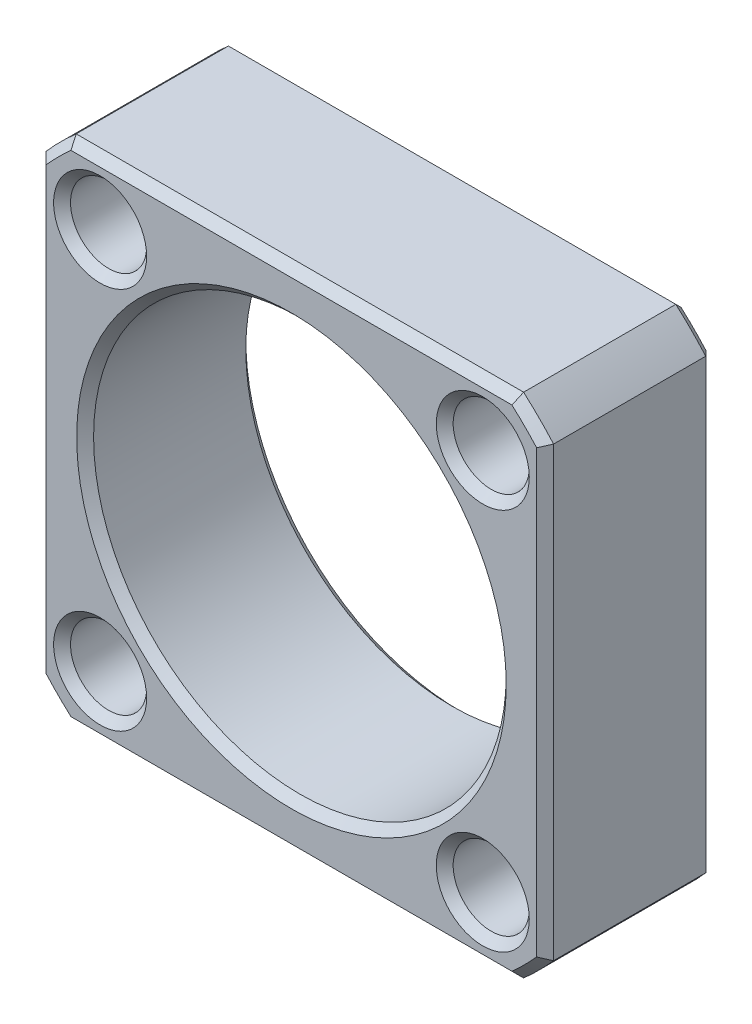
SolidWorks part; units mm, degrees
material "6061 Alloy"
ref_plane "Front Plane" through (0, 0, 0) normal (0, 0, 1) x (1, 0, 0)
ref_plane "Top Plane" through (0, 0, 0) normal (0, 1, 0) x (1, 0, 0)
ref_plane "Right Plane" through (0, 0, 0) normal (1, 0, 0) x (0, 0, -1)
sketch "Sketch1" plane through (0, 0, 0) normal (0, 0, 1) x (1, 0, 0)
  line L0 (-13.2288, 15) -> (13.2288, 15)
  line L1 (-20, 0) -> (20, 0) construction
  line L2 (-13.2288, -15) -> (13.2288, -15)
  line L3 (-15, 13.2288) -> (-15, -13.2288)
  line L4 (0, 15) -> (0, 0) construction
  line L5 (15, 13.2288) -> (15, -13.2288)
  arc A0 (-13.2288, 15) -> (-15, 13.2288) centre (0, 0) ccw
  arc A1 (13.2288, -15) -> (15, -13.2288) centre (0, 0) ccw
  circle A2 centre (0, 0) radius 16 construction
  circle A3 centre (-16, 0) radius 2.25 construction
  circle A4 centre (-11.3137, 11.3137) radius 2.25
  circle A5 centre (0, 16) radius 2.25 construction
  circle A6 centre (11.3137, 11.3137) radius 2.25
  circle A7 centre (16, 0) radius 2.25 construction
  circle A8 centre (11.3137, -11.3137) radius 2.25
  circle A9 centre (0, -16) radius 2.25 construction
  circle A10 centre (-11.3137, -11.3137) radius 2.25
  arc A11 (-15, -13.2288) -> (-13.2288, -15) centre (0, 0) ccw
  arc A12 (15, 13.2288) -> (13.2288, 15) centre (0, 0) ccw
  point P27 (0, 0)
  dimension "D1" = 40
  dimension "D3" = 32
  dimension "D5" = 4.5
  dimension "D2" = 15
  dimension "D6" = 30
  dimension "D4" = 8
extrude "Boss-Extrude1" add sketch "Sketch1" along normal blind 10
sketch "Sketch2" plane through (0, 0, 10) normal (0, 0, 1) x (1, 0, 0)
  circle A0 centre (0, 0) radius 12.2
  dimension "D1" = 24.4
extrude "Cut-Extrude3" cut sketch "Sketch2" against normal through all
chamfer "Chamfer1" distance 0.5 angle 45 26 edges at (-9.0637, -11.3137, 0) (13.5637, 11.3137, 0) (-15, 0, 0) (-14.1421, -14.1421, 0) (0, -15, 0) (14.1421, -14.1421, 0) (15, 0, 0) (14.1421, 14.1421, 0) (0, 15, 0) (-14.1421, 14.1421, 0) (-9.0637, 11.3137, 0) (13.5637, -11.3137, 0) (12.2, 0, 0) (-9.0637, -11.3137, 10) (13.5637, 11.3137, 10) (0, 15, 10) (14.1421, 14.1421, 10) (15, 0, 10) (14.1421, -14.1421, 10) (0, -15, 10) (-14.1421, -14.1421, 10) (-15, 0, 10) (-14.1421, 14.1421, 10) (-9.0637, 11.3137, 10) (13.5637, -11.3137, 10) (12.2, 0, 10)
